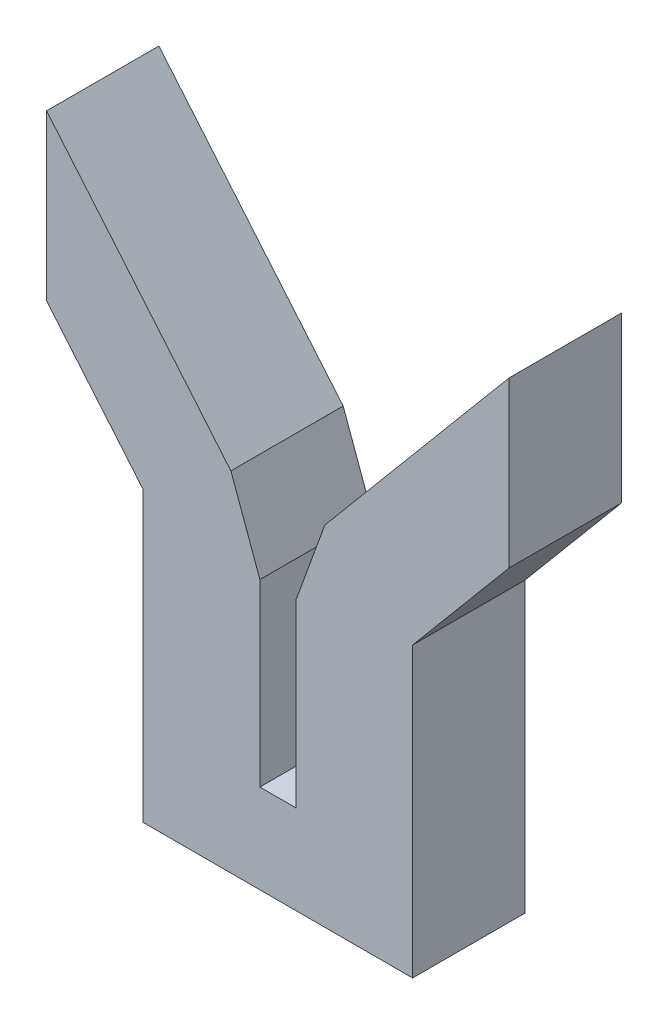
SolidWorks part; units mm, degrees
ref_plane "Front Plane" through (0, 0, 0) normal (0, 0, 1) x (1, 0, 0)
ref_plane "Top Plane" through (0, 0, 0) normal (0, 1, 0) x (1, 0, 0)
ref_plane "Right Plane" through (0, 0, 0) normal (1, 0, 0) x (0, 0, -1)
sketch "Sketch4" plane through (0, 0, 0) normal (0, 0, 1) x (1, 0, 0)
  line L0 (-15, 0) -> (15, 0)
  line L1 (15, 0) -> (15, 29.9091)
  line L2 (15, 29.9091) -> (2, 29.9091)
  line L3 (-15, 29.9091) -> (-15, 0)
  line L4 (0, 0) -> (0, 9.9091) construction
  line L5 (2, 29.9091) -> (2, 9.9091)
  line L6 (2, 9.9091) -> (-2, 9.9091)
  line L7 (2, 29.9091) -> (5.2275, 38.7766)
  line L8 (5.2275, 38.7766) -> (15.2501, 50.721)
  line L9 (15.2501, 50.721) -> (25.7454, 63.2289)
  line L10 (25.7454, 63.2289) -> (25.7454, 44.9085)
  line L11 (25.7454, 44.9085) -> (15, 32.1026)
  line L12 (15, 32.1026) -> (15, 29.9091)
  line L13 (2, 29.9091) -> (2, 49.3423) construction
  line L14 (-2, 29.9091) -> (-15, 29.9091)
  line L15 (-2, 29.9091) -> (-2, 9.9091)
  line L16 (-15, 32.1026) -> (-15, 29.9091)
  line L17 (-25.7454, 44.9085) -> (-15, 32.1026)
  line L18 (-25.7454, 63.2289) -> (-25.7454, 44.9085)
  line L19 (-15.2501, 50.721) -> (-25.7454, 63.2289)
  line L20 (-5.2275, 38.7766) -> (-15.2501, 50.721)
  line L21 (-2, 29.9091) -> (-5.2275, 38.7766)
  point P4 (0, 0)
  point P11 (0, 9.9091)
  dimension "D1" = 30
  dimension "D2" = 2
  dimension "D3" = 20
  dimension "D4" = 20
  dimension "D5" = 40
extrude "Boss-Extrude1" add sketch "Sketch4" along normal blind 12.5 contours L12 L11 L10 L9 L8 L7 L2 | L14 L21 L20 L19 L18 L17 L16 | L15 L14 L3 L0 L1 L2 L5 L6
